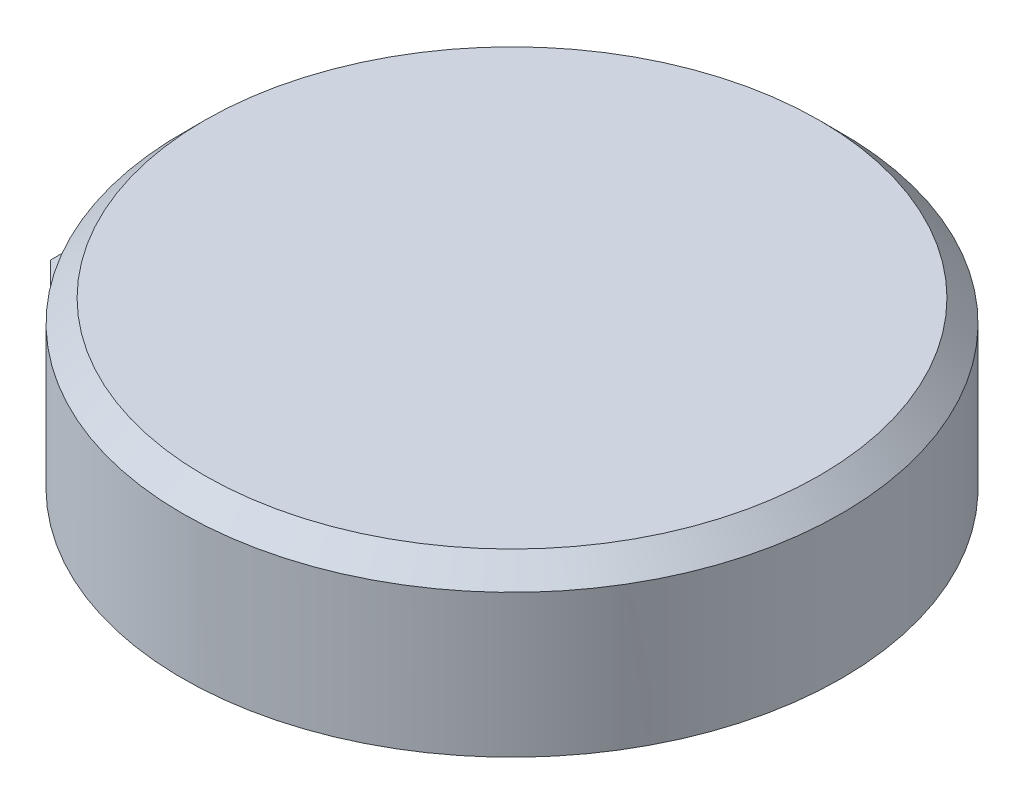
SolidWorks part; units mm, degrees
ref_plane "Front Plane" through (0, 0, 0) normal (0, 0, 1) x (1, 0, 0)
ref_plane "Top Plane" through (0, 0, 0) normal (0, 1, 0) x (1, 0, 0)
ref_plane "Right Plane" through (0, 0, 0) normal (1, 0, 0) x (0, 0, -1)
sketch "Sketch1" plane through (0, 0, 0) normal (0, 1, 0) x (1, 0, 0)
  circle A0 centre (0, 0) radius 150
  dimension "D1" = 300
extrude "Boss-Extrude1" add sketch "Sketch1" along normal blind 75 contours A0
chamfer "Chamfer1" distance 10 angle 45 1 edges at (0, 75, 150)
sketch "Sketch2" plane through (0, 0, 0) normal (0, -1, 0) x (1, 0, 0)
  line L1 (-115, -35) -> (-185, -35)
  line L2 (-115, -35) -> (-115, 35)
  line L3 (-115, 35) -> (-185, 35)
  line L4 (-185, -35) -> (-185, 35)
  line L5 (-115, -35) -> (-185, 35) construction
  line L6 (-115, 35) -> (-185, -35) construction
  circle A0 centre (0, 0) radius 150 construction
  point P0 (-150, 0)
  point P7 (-185, 0)
  point P10 (-187.0506, 44.4009)
  dimension "D1" = 70
  dimension "D2" = 70
extrude "Boss-Extrude2" add sketch "Sketch2" against normal blind 10
chamfer "Chamfer2" distance 10 angle 45 1 edges at (-185, 5, 35)
sketch "Sketch3" plane through (0, 0, 35) normal (0, 0, 1) x (1, 0, 0)
  line L0 (-145.8595, 10) -> (-145.8595, 65)
  line L1 (-150, 65) -> (150, 65) construction
  line L2 (-145.8595, 65) -> (-165.1512, 65)
  line L3 (-165.1512, 65) -> (-175, 10)
  line L4 (-175, 10) -> (-145.8595, 10)
